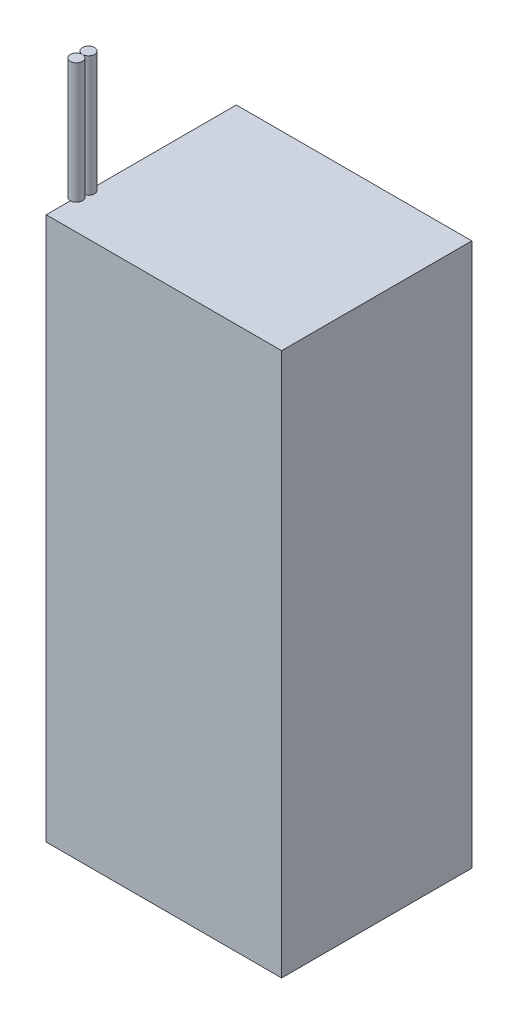
SolidWorks part; units mm, degrees
ref_plane "Front Plane" through (0, 0, 0) normal (0, 0, 1) x (1, 0, 0)
ref_plane "Top Plane" through (0, 0, 0) normal (0, 1, 0) x (1, 0, 0)
ref_plane "Right Plane" through (0, 0, 0) normal (1, 0, 0) x (0, 0, -1)
sketch "Sketch1" plane through (0, 0, 0) normal (0, 1, 0) x (1, 0, 0)
  line L1 (-39, -31.5) -> (39, -31.5)
  line L2 (-39, -31.5) -> (-39, 31.5)
  line L3 (-39, 31.5) -> (39, 31.5)
  line L4 (39, -31.5) -> (39, 31.5)
  line L5 (-39, -31.5) -> (39, 31.5) construction
  line L6 (-39, 31.5) -> (39, -31.5) construction
  point P0 (0, 0)
  dimension "D1" = 63
  dimension "D2" = 78
extrude "Boss-Extrude1" add sketch "Sketch1" along normal blind 180
sketch "Sketch2" plane through (0, 180, 0) normal (0, 1, 0) x (1, 0, 0)
  line L0 (-39, 31.5) -> (-39, -31.5) construction
  line L1 (-39, -31.5) -> (39, -31.5) construction
  circle A1 centre (-39, -21.5) radius 2
  circle A2 centre (-39, -17.5) radius 2
  line M5 (-39, 31.5) -> (-39, -31.5)
  dimension "D1" = 4
  dimension "D2" = 10
extrude "Boss-Extrude4" add sketch "Sketch2" along normal blind 40 separate body contours A1 M5 | A2 M5 | A1 M5 | A2 M5
